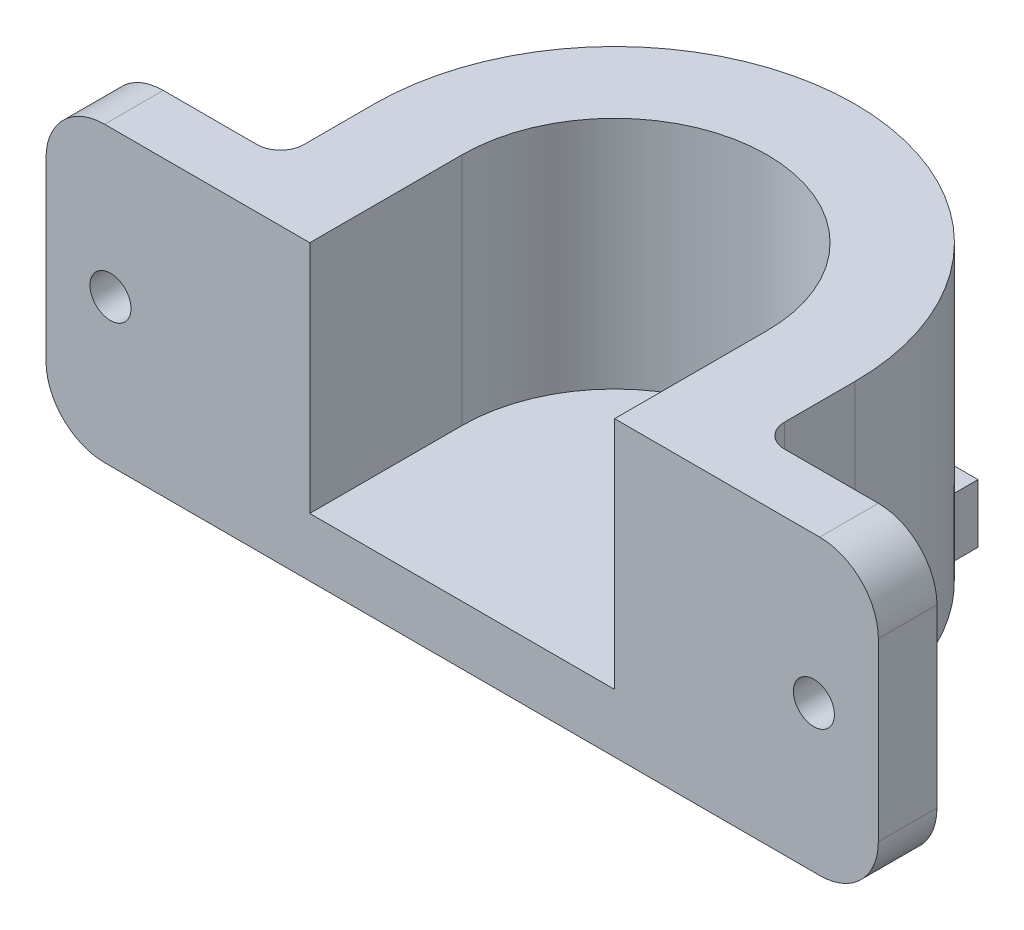
SolidWorks part; units mm, degrees
ref_plane "Front Plane" through (0, 0, 0) normal (0, 0, 1) x (1, 0, 0)
ref_plane "Top Plane" through (0, 0, 0) normal (0, 1, 0) x (1, 0, 0)
ref_plane "Right Plane" through (0, 0, 0) normal (1, 0, 0) x (0, 0, -1)
sketch "Sketch1" plane through (0, 0, 0) normal (0, 1, 0) x (1, 0, 0)
  line L0 (-7.5, 0) -> (-7.5, -8)
  line L1 (-7.5, -8) -> (-22.5, -8)
  line L2 (-22.5, -8) -> (-22.5, -13)
  line L3 (-22.5, -13) -> (0, -13)
  line L4 (0, -13) -> (0, 0)
  line L5 (-7.5, 0) -> (0, 0) construction
  line L6 (13, 0) -> (26, 0) construction
  line L7 (26, 0) -> (33.5, 0) construction
  line L8 (0, 0) -> (13, 0) construction
  line L9 (26, 0) -> (26, -13)
  line L10 (26, -13) -> (48.5, -13)
  line L11 (48.5, -13) -> (48.5, -8)
  line L12 (48.5, -8) -> (33.5, -8)
  line L13 (33.5, -8) -> (33.5, 0)
  arc A0 (-7.5, 0) -> (33.5, 0) centre (13, 0) cw
  arc A1 (0, 0) -> (26, 0) centre (13, 0) cw
  dimension "D1" = 13
  dimension "D2" = 7.5
  dimension "D3" = 5
  dimension "D4" = 15
  dimension "D5" = 13
extrude "Boss-Extrude1" add sketch "Sketch1" along normal blind 25
sketch "Sketch4" plane through (0, 0, 8) normal (0, 0, -1) x (-1, 0, 0)
  line L0 (-48.5, 12.5) -> (-33.5, 12.5) construction
  line L1 (-48.5, 25) -> (-48.5, 0) construction
  line L2 (-33.5, 25) -> (-33.5, 0) construction
  line L3 (-13, 25) -> (-13, 0) construction
  line L4 (7.5, 25) -> (-33.5, 25) construction
  line L5 (-33.5, 0) -> (7.5, 0) construction
  circle A0 centre (-43, 12.5) radius 1.75
  circle A1 centre (17, 12.5) radius 1.75
  dimension "D1" = 3.5
  dimension "D2" = 30
extrude "Cut-Extrude1" cut sketch "Sketch4" against normal through all
fillet "Fillet1" radius 5 4 edges at (48.5, 25, 10.5) (48.5, 0, 10.5) (-22.5, 25, 10.5) (-22.5, 0, 10.5)
fillet "Fillet2" radius 2 2 edges at (33.5, 12.5, 8) (-7.5, 12.5, 8)
sketch "Sketch5" plane through (0, 0, 13) normal (0, 0, 1) x (1, 0, 0)
  line L0 (26, 25) -> (26, 0) construction
  line L1 (0, 0) -> (26, 0)
  line L2 (0, 0) -> (0, 5)
  line L3 (0, 5) -> (26, 5)
  line L4 (26, 0) -> (26, 5)
  dimension "D1" = 5
extrude "Boss-Extrude2" add sketch "Sketch5" against normal blind 31
equation "\"D5@Sketch1\" = \"Diamter\" / 2"
equation "\"D1@Sketch1\" = \"Diamter\" / 2"
equation "\"Diamter\"= 26"
